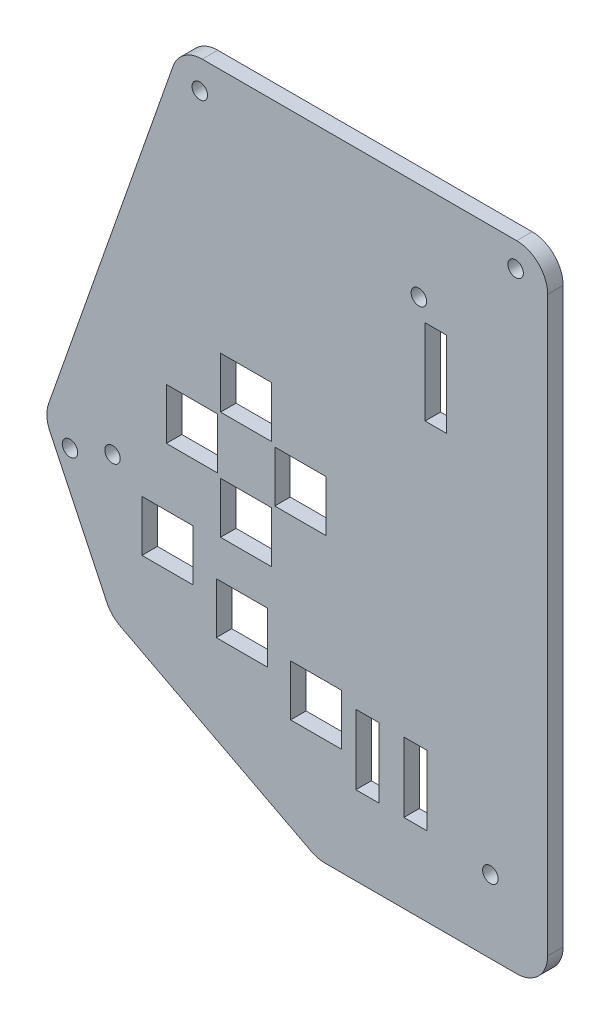
SolidWorks part; units mm, degrees
ref_plane "Front Plane" through (0, 0, 0) normal (0, 0, 1) x (1, 0, 0)
ref_plane "Top Plane" through (0, 0, 0) normal (0, 1, 0) x (1, 0, 0)
ref_plane "Right Plane" through (0, 0, 0) normal (1, 0, 0) x (0, 0, -1)
sketch "Sketch1" plane through (0, 0, 0) normal (0, 0, 1) x (1, 0, 0)
  line L6 (-20.066, -57.15) -> (46.99, -57.15) construction
  line L7 (-12.446, -73.152) -> (46.99, -73.152) construction
  line L8 (-3.3141, 6.35) -> (48.26, 6.35)
  line L9 (53.34, 1.27) -> (53.34, -92.71)
  line L10 (48.26, -97.79) -> (16.847, -97.79)
  line L16 (-8.1072, 2.9529) -> (-28.5162, -55.1739)
  line L18 (-20.066, -57.15) -> (-29.21, -57.15) construction
  line L26 (0, 0) -> (46.99, 0) construction
  line L27 (46.99, 0) -> (46.99, -88.9) construction
  line L28 (46.99, -88.9) -> (17.78, -88.9) construction
  line L29 (17.78, -88.9) -> (-12.446, -73.152) construction
  line L30 (-12.446, -73.152) -> (-20.066, -57.15) construction
  line L31 (-20.066, -57.15) -> (0, 0) construction
  line L32 (46.99, -57.15) -> (46.99, -88.9) construction
  line L33 (17.78, -88.9) -> (15.603, -97.79) construction
  line L34 (-12.446, -73.152) -> (-17.9301, -78.4424) construction
  line L35 (14.4997, -97.2152) -> (-16.7505, -80.9336)
  line L36 (-28.3096, -59.0409) -> (-18.9898, -78.6124)
  arc A0 (53.34, -92.71) -> (48.26, -97.79) centre (48.26, -92.71) cw
  arc A1 (14.4997, -97.2152) -> (16.847, -97.79) centre (16.847, -92.71) ccw
  arc A2 (-16.7505, -80.9336) -> (-18.9898, -78.6124) centre (-14.4033, -76.4284) cw
  arc A3 (-28.5162, -55.1739) -> (-28.3096, -59.0409) centre (-23.723, -56.8568) ccw
  arc A4 (-8.1072, 2.9529) -> (-3.3141, 6.35) centre (-3.3141, 1.27) cw
  arc A5 (48.26, 6.35) -> (53.34, 1.27) centre (48.26, 1.27) cw
  point P13 (53.34, -97.79)
  point P32 (53.34, 6.35)
  dimension "D8" = 5.08
  dimension "D1" = 88.9
  dimension "D2" = 29.21
  dimension "D3" = 59.436
  dimension "D4" = 67.056
  dimension "D5" = 104.14
  dimension "D6" = 82.55
  dimension "D7" = 46.99
  dimension "D9" = 61.6057
  dimension "D13" = 103.76
  dimension "D17" = 108.51
sketch "Sketch3" plane through (0, 0, 0) normal (0, 0, 1) x (1, 0, 0)
  line L6 (-20.066, -57.15) -> (46.99, -57.15) construction
  line L7 (-12.446, -73.152) -> (46.99, -73.152) construction
  line L8 (0, 0) -> (46.99, 0) construction
  line L9 (46.99, 0) -> (46.99, -88.9) construction
  line L10 (46.99, -88.9) -> (17.78, -88.9) construction
  line L11 (17.78, -88.9) -> (-12.446, -73.152) construction
  line L12 (-12.446, -73.152) -> (-20.066, -57.15) construction
  line L13 (-20.066, -57.15) -> (0, 0) construction
  line L14 (3.8784, -55.88) -> (3.8784, -38.1) construction
  circle A0 centre (3.8784, -38.1) radius 5.08
  circle A1 centre (-5.0116, -46.99) radius 5.08
  circle A2 centre (3.8784, -55.88) radius 5.08
  circle A3 centre (12.7684, -46.99) radius 5.08
  circle A4 centre (-9.144, -65.024) radius 5.08
  circle A5 centre (3.048, -70.612) radius 5.08
  circle A6 centre (15.24, -76.2) radius 5.08
  dimension "D7" = 10.16
  dimension "D1" = 43.1116
  dimension "D2" = 8.89
  dimension "D3" = 8.89
  dimension "D4" = 46.99
  dimension "D5" = 8.89
  dimension "D6" = 8.89
  dimension "D8" = 12.192
  dimension "D9" = 5.588
  dimension "D10" = 5.588
  dimension "D11" = 12.192
  dimension "D12" = 43.942
  dimension "D13" = 70.612
sketch "Sketch10" plane through (0, 0, 0) normal (0, 0, 1) x (1, 0, 0)
  line L1 (53.34, 1.27) -> (53.34, -92.71)
  line L6 (48.26, -97.79) -> (16.847, -97.79)
  line L16 (-8.1072, 2.9529) -> (-28.5162, -55.1739)
  line L19 (53.34, 1.27) -> (53.34, -92.71) construction
  line L21 (-8.1072, 2.9529) -> (-28.5162, -55.1739) construction
  line L24 (14.4997, -97.2152) -> (-16.7505, -80.9336)
  line L25 (-18.9898, -78.6124) -> (-28.3096, -59.0409)
  line L26 (-3.3141, 6.35) -> (48.26, 6.35)
  arc A0 (-18.9898, -78.6124) -> (-16.7505, -80.9336) centre (-14.4033, -76.4284) ccw
  arc A1 (16.847, -97.79) -> (14.4997, -97.2152) centre (16.847, -92.71) cw
  arc A2 (-28.5162, -55.1739) -> (-28.3096, -59.0409) centre (-23.723, -56.8568) ccw
  arc A3 (53.34, -92.71) -> (48.26, -97.79) centre (48.26, -92.71) cw
  arc A4 (-8.1072, 2.9529) -> (-3.3141, 6.35) centre (-3.3141, 1.27) cw
  arc A5 (48.26, 6.35) -> (53.34, 1.27) centre (48.26, 1.27) cw
  point P13 (15.603, -97.79)
  point P17 (-29.21, -57.15)
  point P20 (53.34, -97.79)
  dimension "D1" = 5.08
extrude "Boss-Extrude1" add sketch "Sketch10" along normal blind 2.54
sketch "Sketch11" plane through (0, 0, 2.54) normal (0, 0, 1) x (1, 0, 0)
  line L0 (46.99, -88.9) -> (17.78, -88.9) construction
  line L5 (33.561, -73.406) -> (29.751, -73.406)
  line L6 (33.561, -73.406) -> (33.561, -84.836)
  line L11 (33.561, -84.836) -> (29.751, -84.836)
  line L12 (29.751, -73.406) -> (29.751, -84.836)
  line L18 (46.99, 0) -> (46.99, -88.9) construction
  line L23 (25.687, -73.406) -> (21.877, -73.406)
  line L24 (25.687, -73.406) -> (25.687, -84.836)
  line L29 (25.687, -84.836) -> (21.877, -84.836)
  line L30 (21.877, -73.406) -> (21.877, -84.836)
  line L42 (8.0694, -51.689) -> (-0.3126, -51.689)
  line L43 (8.0694, -51.689) -> (8.0694, -60.071)
  line L44 (8.0694, -60.071) -> (-0.3126, -60.071)
  line L45 (-0.3126, -51.689) -> (-0.3126, -60.071)
  line L46 (-0.8206, -42.799) -> (-9.2026, -42.799)
  line L47 (-0.8206, -42.799) -> (-0.8206, -51.181)
  line L48 (-0.8206, -51.181) -> (-9.2026, -51.181)
  line L49 (-9.2026, -42.799) -> (-9.2026, -51.181)
  line L52 (8.0694, -42.291) -> (-0.3126, -42.291)
  line L53 (-0.3126, -33.909) -> (-0.3126, -42.291)
  line L54 (16.9594, -42.799) -> (8.5774, -42.799)
  line L55 (16.9594, -42.799) -> (16.9594, -51.181)
  line L56 (16.9594, -51.181) -> (8.5774, -51.181)
  line L57 (8.5774, -42.799) -> (8.5774, -51.181)
  line L58 (-0.3126, -33.909) -> (8.0694, -33.909)
  line L59 (8.0694, -33.909) -> (8.0694, -42.291)
  line L60 (3.8784, -51.689) -> (3.8784, -60.071) construction
  line L61 (-0.3126, -55.88) -> (8.0694, -55.88) construction
  line L62 (-5.0116, -51.181) -> (-5.0116, -42.799) construction
  line L63 (-9.2026, -46.99) -> (-0.8206, -46.99) construction
  line L64 (12.7684, -42.799) -> (12.7684, -51.181) construction
  line L65 (8.5774, -46.99) -> (16.9594, -46.99) construction
  line L66 (3.8784, -33.909) -> (3.8784, -42.291) construction
  line L67 (-0.3126, -38.1) -> (8.0694, -38.1) construction
  line L68 (-4.826, -60.706) -> (-4.826, -69.088)
  line L69 (-13.208, -65.024) -> (-5.08, -65.024) construction
  line L70 (-9.144, -60.96) -> (-9.144, -69.088) construction
  line L71 (-4.826, -69.088) -> (-13.208, -69.088)
  line L72 (-13.208, -60.706) -> (-13.208, -69.088)
  line L73 (-4.826, -60.706) -> (-13.208, -60.706)
  line L74 (7.366, -66.294) -> (7.366, -74.676)
  line L75 (-1.016, -70.612) -> (7.112, -70.612) construction
  line L76 (3.048, -66.548) -> (3.048, -74.676) construction
  line L77 (7.366, -74.676) -> (-1.016, -74.676)
  line L78 (-1.016, -66.294) -> (-1.016, -74.676)
  line L79 (7.366, -66.294) -> (-1.016, -66.294)
  line L80 (19.558, -71.882) -> (19.558, -80.264)
  line L81 (11.176, -76.2) -> (19.304, -76.2) construction
  line L82 (15.24, -72.136) -> (15.24, -80.264) construction
  line L83 (19.558, -80.264) -> (11.176, -80.264)
  line L84 (11.176, -71.882) -> (11.176, -80.264)
  line L85 (19.558, -71.882) -> (11.176, -71.882)
  dimension "D1" = 4.064
  dimension "D3" = 13.429
  dimension "D4" = 11.43
  dimension "D5" = 3.81
  dimension "D6" = 4.064
  dimension "D7" = 11.43
  dimension "D8" = 4.064
  dimension "D9" = 2.319
  dimension "D10" = 4.572
  dimension "D11" = 8.382
  dimension "D12" = 3.81
  dimension "D13" = 3.81
  dimension "D14" = 5.588
  dimension "D15" = 5.588
  dimension "D16" = 3.81
  dimension "D17" = 0.508
  dimension "D18" = 8.382
  dimension "D21" = 8.382
  dimension "D22" = 8.382
extrude "Cut-Extrude1" cut sketch "Sketch11" against normal through all both and the other way through all
sketch "Sketch12" plane through (0, 0, 0) normal (0, 0, -1) x (-1, 0, 0)
  line L0 (20.066, -57.15) -> (-46.99, -57.15) construction
  line L2 (-46.99, 0) -> (-46.99, -88.9) construction
  line L5 (18.034, -57.15) -> (20.066, -57.15) construction
  line L10 (-46.99, -88.9) -> (-17.78, -88.9) construction
  circle A2 centre (18.034, -57.15) radius 1.27
  circle A3 centre (-43.942, -85.852) radius 1.27
  dimension "D1" = 2.54
  dimension "D6" = 2.032
  dimension "D2" = 2.54
  dimension "D11" = 3.048
  dimension "D12" = 3.048
extrude "Cut-Extrude2" cut sketch "Sketch12" against normal through all both and the other way through all
sketch "Sketch13" plane through (0, 0, 0) normal (0, 0, -1) x (-1, 0, 0)
  line L0 (28.3096, -59.0409) -> (18.9898, -78.6124) construction
  line L1 (8.1072, 2.9529) -> (28.5162, -55.1739) construction
  line L2 (3.3141, 6.35) -> (-48.26, 6.35) construction
  line L4 (-53.34, 1.27) -> (-53.34, -92.71) construction
  circle A1 centre (25.0123, -59.762) radius 1.27
  circle A4 centre (-48.0822, 2.286) radius 1.27
  circle A5 centre (3.7187, 1.651) radius 1.27
  dimension "D1" = 2.54
  dimension "D2" = 4.826
  dimension "D4" = 4.064
  dimension "D3" = 2.667
  dimension "D5" = 5.2578
  dimension "D6" = 4.699
  dimension "D7" = 4.572
extrude "Cut-Extrude3" cut sketch "Sketch13" against normal through all both and the other way through all
sketch "Sketch14" plane through (0, 0, 0) normal (0, 0, -1) x (-1, 0, 0)
  line L0 (-36.7885, -26.7831) -> (-33.2325, -26.7831)
  line L1 (-36.7885, -12.8131) -> (-36.7885, -26.7831)
  line L2 (-33.2325, -12.8131) -> (-36.7885, -12.8131)
  line L3 (-33.2325, -12.8131) -> (-33.2325, -26.7831)
  line L4 (-53.34, 1.27) -> (-53.34, -92.71) construction
  line L5 (3.3141, 6.35) -> (-48.26, 6.35) construction
  dimension "D1" = 16.5515
  dimension "D2" = 13.97
  dimension "D3" = 19.1631
  dimension "D4" = 3.556
extrude "Cut-Extrude4" cut sketch "Sketch14" against normal through all both and the other way through all
sketch "Sketch16" plane through (0, 0, 0) normal (0, 0, -1) x (-1, 0, 0)
  line L0 (3.3141, 6.35) -> (-48.26, 6.35) construction
  line L1 (-53.34, 1.27) -> (-53.34, -92.71) construction
  circle A0 centre (-32.219, -9.6761) radius 1.27
  dimension "D1" = 16.0261
  dimension "D2" = 2.54
  dimension "D3" = 21.121
extrude "Cut-Extrude5" cut sketch "Sketch16" against normal through all both and the other way through all
